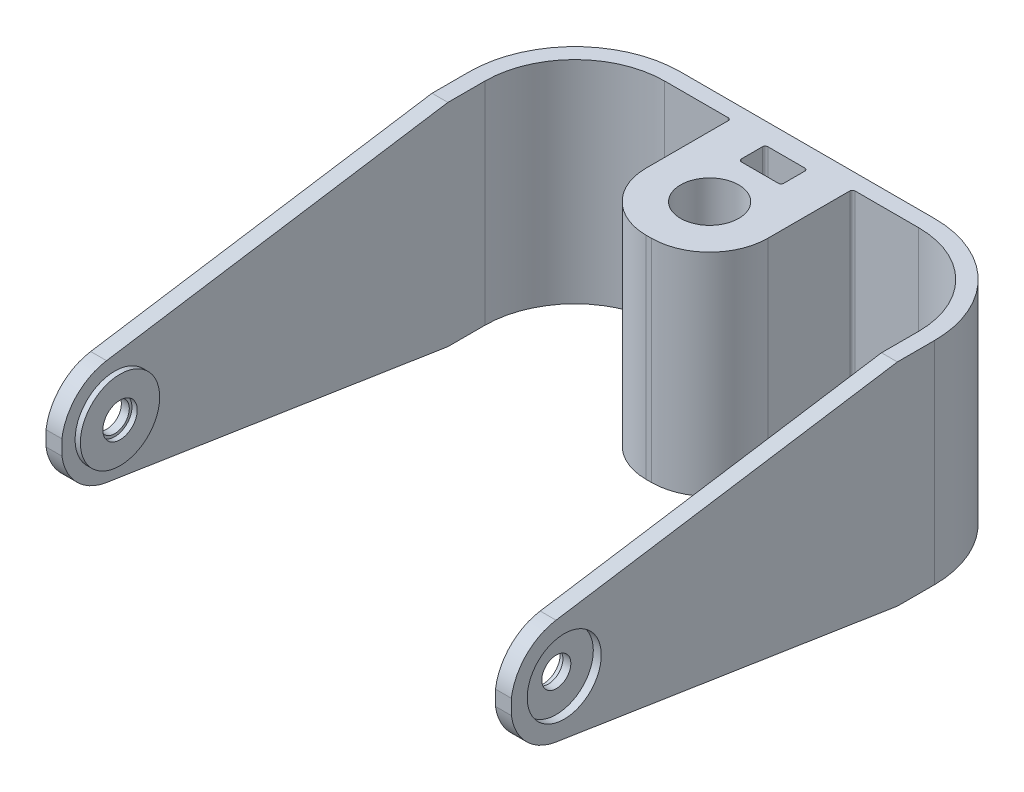
SolidWorks part; units mm, degrees
ref_plane "Front Plane" through (0, 0, 0) normal (0, 0, 1) x (1, 0, 0)
ref_plane "Top Plane" through (0, 0, 0) normal (0, 1, 0) x (1, 0, 0)
ref_plane "Right Plane" through (0, 0, 0) normal (1, 0, 0) x (0, 0, -1)
sketch "Sketch1" plane through (0, 0, 0) normal (0, 0, 1) x (1, 0, 0)
  line L1 (0, 0) -> (88, 0)
  line L2 (0, 0) -> (0, 40)
  line L3 (0, 40) -> (88, 40)
  line L4 (88, 0) -> (88, 40)
extrude "Boss-Extrude1" add sketch "Sketch1" along normal blind 100
sketch "Sketch2" plane through (0, 0, 0) normal (0, -1, 0) x (1, 0, 0)
  line L1 (20, 3) -> (32, 3)
  line L6 (0, 20) -> (0, 0)
  line L7 (3, 100) -> (85, 100)
  line L8 (3, 100) -> (3, 20)
  line L10 (85, 100) -> (85, 20)
  line L11 (0, 0) -> (20, 0)
  line L12 (68, 0) -> (88, 0)
  line L13 (88, 0) -> (88, 20)
  line L14 (40.5, 9) -> (47.5, 9)
  line L15 (40, 8.5) -> (40, 4.5)
  line L16 (43.5, 30) -> (44.5, 30)
  line L20 (40.5, 4) -> (47.5, 4)
  line L21 (48, 8.5) -> (48, 4.5)
  line L22 (32.5, 3.5) -> (32.5, 19)
  line L23 (55.5, 19) -> (55.5, 3.5)
  line L24 (56, 3) -> (68, 3)
  arc A0 (85, 20) -> (68, 3) centre (68, 20) cw
  arc A1 (3, 20) -> (20, 3) centre (20, 20) ccw
  arc A2 (0, 20) -> (20, 0) centre (20, 20) ccw
  arc A3 (88, 20) -> (68, 0) centre (68, 20) cw
  circle A4 centre (44, 18.5) radius 5.5
  arc A5 (44.5, 30) -> (55.5, 19) centre (44.5, 19) cw
  arc A6 (43.5, 30) -> (32.5, 19) centre (43.5, 19) ccw
  arc A9 (47.5, 4) -> (48, 4.5) centre (47.5, 4.5) ccw
  arc A10 (47.5, 9) -> (48, 8.5) centre (47.5, 8.5) cw
  arc A11 (40.5, 9) -> (40, 8.5) centre (40.5, 8.5) ccw
  arc A12 (40, 4.5) -> (40.5, 4) centre (40.5, 4.5) ccw
  arc A13 (55.5, 3.5) -> (56, 3) centre (56, 3.5) ccw
  arc A14 (32, 3) -> (32.5, 3.5) centre (32, 3.5) ccw
extrude "Cut-Extrude1" cut sketch "Sketch2" against normal up to surface (40 mm away) up to face at (44, 40, 50)
sketch "Sketch3" plane through (0, 0, 0) normal (0, 0, -1) x (-1, 0, 0)
  circle A0 centre (-44, 20) radius 2.75
extrude "Cut-Extrude2" cut sketch "Sketch3" against normal up to surface (13.7369 mm away)
sketch "Sketch5" plane through (88, 0, 0) normal (1, 0, 0) x (0, 0, -1)
  line L0 (-27, 0) -> (-100, 0)
  line L2 (-27, 0) -> (-91.5492, 10.0195)
  line L8 (-100, 40) -> (-27, 40)
  line L9 (-100, 0) -> (-100, 18.5823)
  line L10 (-27, 40) -> (-91.5492, 29.9805)
  line L12 (-100, 21.4177) -> (-100, 40)
  circle A0 centre (-90, 20) radius 2.75
  arc A2 (-100, 18.5823) -> (-91.5492, 10.0195) centre (-90, 20) ccw
  arc A3 (-91.5492, 29.9805) -> (-100, 21.4177) centre (-90, 20) ccw
extrude "Cut-Extrude3" cut sketch "Sketch5" against normal up to surface (3 mm away) up to face at (85, 20, 60)
sketch "Sketch6" plane through (0, 0, 0) normal (-1, 0, 0) x (0, 0, 1)
  line L3 (100, 0) -> (100, 18.5823)
  line L6 (100, 21.4177) -> (100, 40)
  line L7 (27, 40) -> (91.5492, 29.9805)
  line L8 (100, 40) -> (27, 40)
  line L9 (27, 0) -> (91.5492, 10.0195)
  line L10 (27, 0) -> (100, 0)
  arc A3 (91.5492, 29.9805) -> (100, 21.4177) centre (90, 20) cw
  arc A4 (100, 18.5823) -> (91.5492, 10.0195) centre (90, 20) cw
  circle A5 centre (90, 20) radius 2.75
extrude "Cut-Extrude4" cut sketch "Sketch6" against normal up to surface (3 mm away) up to face at (3, 20, 60)
sketch "Sketch7" plane through (3, 0, 0) normal (1, 0, 0) x (0, 0, -1)
  circle A0 centre (-90, 20) radius 7.5
  circle A1 centre (-90, 20) radius 3.25
extrude "Boss-Extrude2" add sketch "Sketch7" along normal blind 1
sketch "Sketch8" plane through (85, 0, 0) normal (-1, 0, 0) x (0, 0, 1)
  circle A0 centre (90, 20) radius 7.5
  circle A1 centre (90, 20) radius 3.25
extrude "Boss-Extrude3" add sketch "Sketch8" along normal blind 1
sketch "Sketch9" plane through (88, 0, 0) normal (1, 0, 0) x (0, 0, -1)
  circle A0 centre (-90, 20) radius 7
extrude "Cut-Extrude5" cut sketch "Sketch9" against normal blind 1.5
sketch "Sketch10" plane through (0, 0, 0) normal (-1, 0, 0) x (0, 0, 1)
  circle A0 centre (90, 20) radius 7
extrude "Cut-Extrude6" cut sketch "Sketch10" against normal blind 1.5
